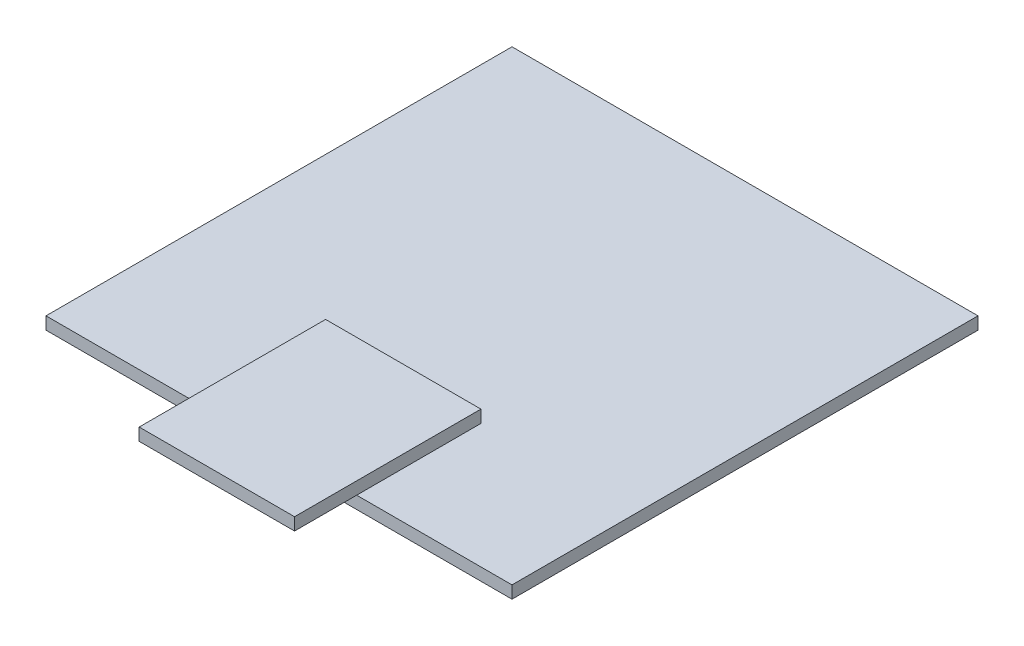
SolidWorks part; units mm, degrees
material "Cardboard"
ref_plane "Front Plane" through (0, 0, 0) normal (0, 0, 1) x (1, 0, 0)
ref_plane "Top Plane" through (0, 0, 0) normal (0, 1, 0) x (1, 0, 0)
ref_plane "Right Plane" through (0, 0, 0) normal (1, 0, 0) x (0, 0, -1)
sketch "Sketch1" plane through (0, 0, 0) normal (0, 1, 0) x (1, 0, 0)
  line L1 (0, 0) -> (150, 0)
  line L2 (0, 0) -> (0, 150)
  line L3 (0, 150) -> (150, 150)
  line L4 (150, 0) -> (150, 150)
  dimension "D1" = 150
  dimension "D2" = 150
extrude "Boss-Extrude1" add sketch "Sketch1" along normal blind 4
sketch "Sketch2" plane through (0, 4, 0) normal (0, 1, 0) x (1, 0, 0)
  line L0 (0, 0) -> (150, 0) construction
  line L8 (50, 40) -> (100, 40)
  line L9 (50, 40) -> (50, -20)
  line L10 (50, -20) -> (100, -20)
  line L11 (100, 40) -> (100, -20)
  point P6 (75, -20)
  point P7 (75, 0)
  dimension "D1" = 50
  dimension "D2" = 20
  dimension "D3" = 40
extrude "Boss-Extrude2" add sketch "Sketch2" along normal blind 4
